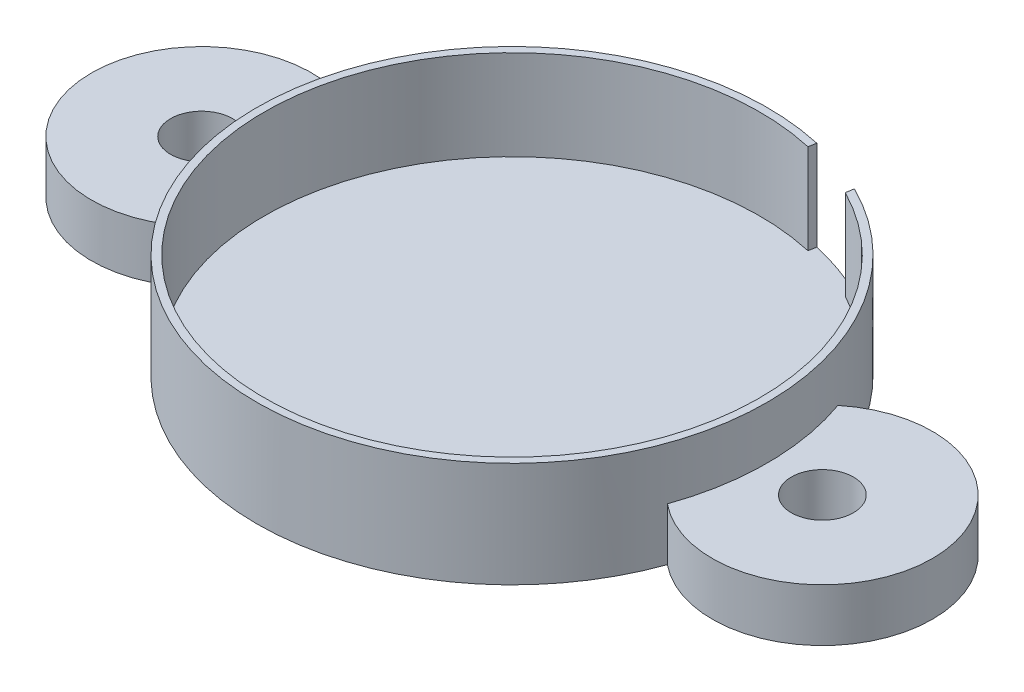
SolidWorks part; units mm, degrees
ref_plane "Front Plane" through (0, 0, 0) normal (0, 0, 1) x (1, 0, 0)
ref_plane "Top Plane" through (0, 0, 0) normal (0, 1, 0) x (1, 0, 0)
ref_plane "Right Plane" through (0, 0, 0) normal (1, 0, 0) x (0, 0, -1)
sketch "Sketch1" plane through (0, 0, 0) normal (0, 1, 0) x (1, 0, 0)
  circle A0 centre (0, 0) radius 53.2765
  dimension "D1" = 106.553
extrude "Boss-Extrude1" add sketch "Sketch1" along normal blind 21.971 contours A0
sketch "Sketch3" plane through (0, 21.971, 0) normal (0, 1, 0) x (1, 0, 0)
  circle A0 centre (0, 0) radius 51.689
  dimension "D1" = 103.378
extrude "Cut-Extrude2" cut sketch "Sketch3" against normal blind 18.796
sketch "Sketch6" plane through (0, 21.971, 0) normal (0, 1, 0) x (1, 0, 0)
  line L0 (23.5167, 46.0296) -> (23.7886, 47.6706)
  line L1 (11.3334, 50.4312) -> (11.6118, 51.9957)
  arc A0 (23.7886, 47.6706) -> (11.6118, 51.9957) centre (0, 0) ccw
  circle A1 centre (0, 0) radius 53.2765 construction
  circle A2 centre (0, 0) radius 53.2765 construction
  arc A3 (23.5167, 46.0296) -> (11.3334, 50.4312) centre (0, 0) ccw
  circle A4 centre (0, 0) radius 51.689 construction
  dimension "D1" = 12.954
  dimension "D2" = 12.954
extrude "Cut-Extrude7" cut sketch "Sketch6" against normal blind 18.796
sketch "Sketch7" plane through (0, 0, 0) normal (0, -1, 0) x (1, 0, 0)
  arc A7 (50.2172, -17.7938) -> (50.2172, 17.7938) centre (64.77, 0) ccw
  arc A8 (-50.2172, 17.7938) -> (-50.2172, -17.7938) centre (-64.77, 0) ccw
  circle A9 centre (-64.77, 0) radius 6.477
  circle A10 centre (64.77, 0) radius 6.477
  arc A12 (-50.2172, -17.7938) -> (-50.2172, 17.7938) centre (0, 0) cw
  arc A13 (50.2172, 17.7938) -> (50.2172, -17.7938) centre (0, 0) cw
  dimension "D4" = 45.974
  dimension "D5" = 12.954
  dimension "D6" = 12.954
  dimension "D1" = 45.974
extrude "Boss-Extrude3" add sketch "Sketch7" against normal blind 10.9855
